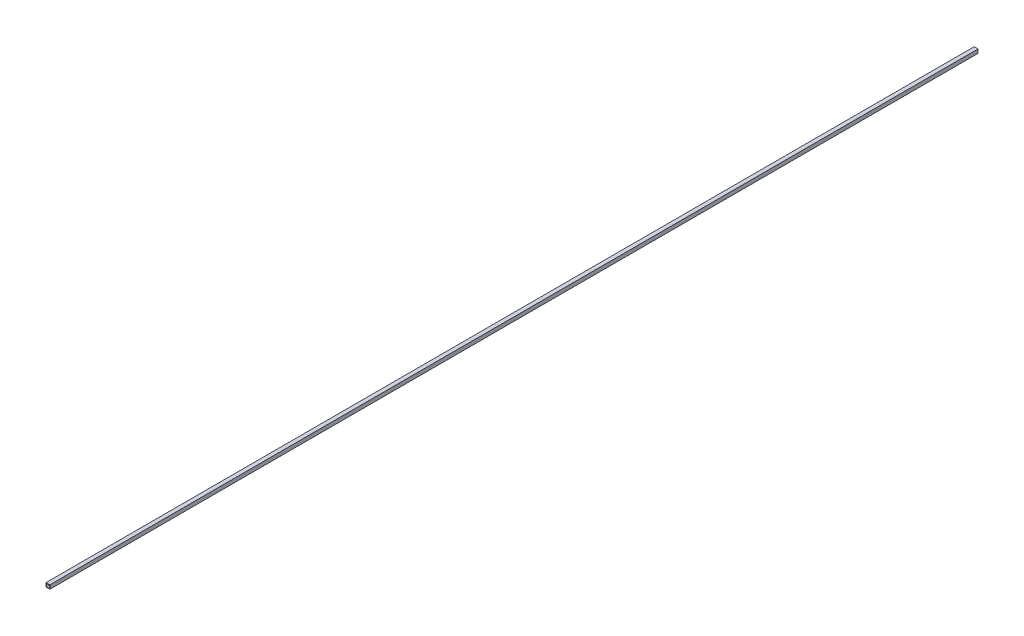
SolidWorks part; units mm, degrees
material "6061-T6 (SS)"
ref_plane "Front Plane" through (0, 0, 0) normal (0, 0, 1) x (1, 0, 0)
ref_plane "Top Plane" through (0, 0, 0) normal (0, 1, 0) x (1, 0, 0)
ref_plane "Right Plane" through (0, 0, 0) normal (1, 0, 0) x (0, 0, -1)
sketch "Sketch1" plane through (0, 0, 0) normal (0, 0, 1) x (1, 0, 0)
  line L1 (-3.175, -3.175) -> (3.175, -3.175)
  line L2 (-3.175, -3.175) -> (-3.175, 3.175)
  line L3 (-3.175, 3.175) -> (3.175, 3.175)
  line L4 (3.175, -3.175) -> (3.175, 3.175)
  line L5 (-3.175, -3.175) -> (3.175, 3.175) construction
  line L6 (-3.175, 3.175) -> (3.175, -3.175) construction
  circle A0 centre (0, 0) radius 2.54
  point P0 (0, 0)
  dimension "D3" = 5.08
  dimension "D1" = 6.35
  dimension "D2" = 6.35
extrude "Boss-Extrude1" add sketch "Sketch1" along normal blind 1524
